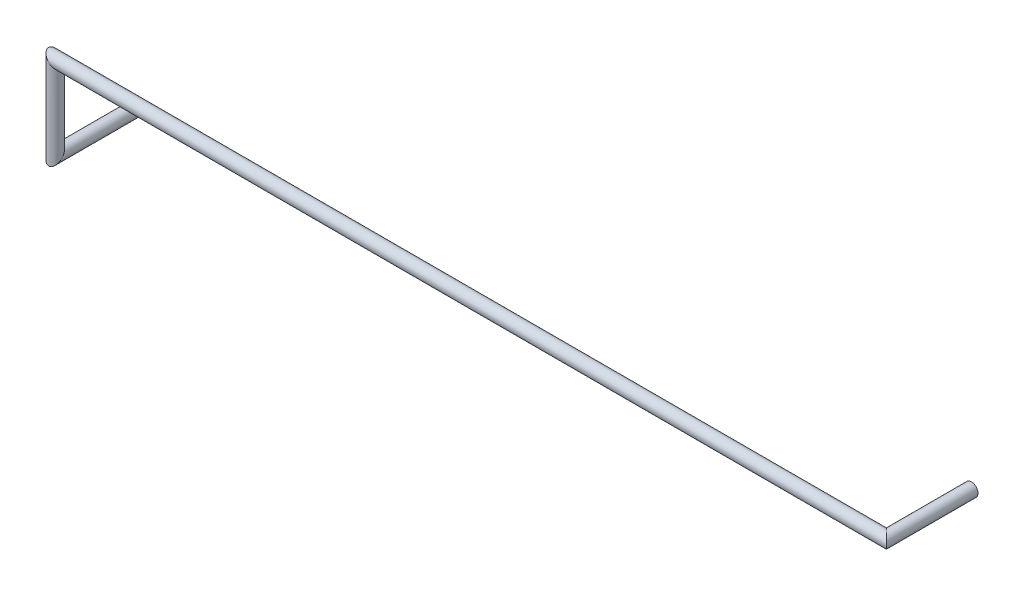
SolidWorks part; units mm, degrees
ref_plane "Front Plane" through (0, 0, 0) normal (0, 0, 1) x (1, 0, 0)
ref_plane "Top Plane" through (0, 0, 0) normal (0, 1, 0) x (1, 0, 0)
ref_plane "Right Plane" through (0, 0, 0) normal (1, 0, 0) x (0, 0, -1)
sketch3d "3DSketch3"
  line L0 (0, 0, 0) -> (0, 0, 2.6)
  line L1 (0, 0, 2.6) -> (0, 2.54, 2.6)
  line L2 (0, 2.54, 2.6) -> (25.4, 2.54, 2.6)
  line L3 (25.4, 2.54, 2.6) -> (25.4, 2.54, 0)
  dimension "D2" = 2.6
  dimension "D1" = 2.6
  dimension "D3" = 2.54
  dimension "D4" = 25.4
sweep "Sweep1" add path "3DSketch3" circular profile diameter 0.4 parameters "D3"=0.4
equation "\"D2@3DSketch3\"=\"D1@3DSketch3\""
equation "\"D3@3DSketch3\"=2.54*1"
equation "\"D4@3DSketch3\"=2.54*10"
